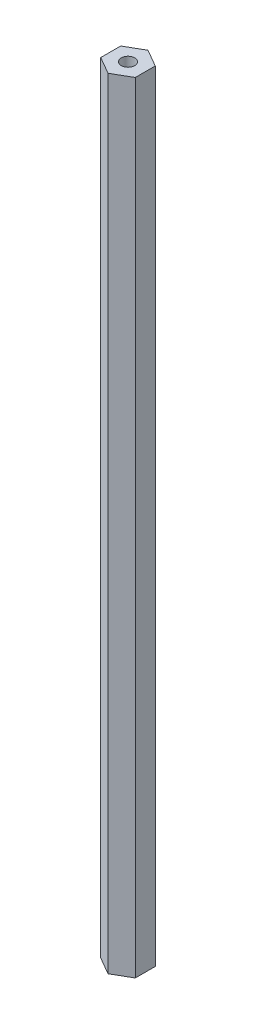
SolidWorks part; units mm, degrees
ref_plane "Front Plane" through (0, 0, 0) normal (0, 0, 1) x (1, 0, 0)
ref_plane "Top Plane" through (0, 0, 0) normal (0, 1, 0) x (1, 0, 0)
ref_plane "Right Plane" through (0, 0, 0) normal (1, 0, 0) x (0, 0, -1)
sketch "Sketch1" plane through (0, 0, 0) normal (0, 1, 0) x (1, 0, 0)
  line L0 (0, 7.3323) -> (0, 0) construction
  line L1 (0, 7.3323) -> (-6.35, 3.6662)
  line L2 (-6.35, 3.6662) -> (-6.35, -3.6662)
  line L3 (-6.35, -3.6662) -> (0, -7.3323)
  line L4 (0, -7.3323) -> (6.35, -3.6662)
  line L5 (6.35, -3.6662) -> (6.35, 3.6662)
  line L6 (6.35, 3.6662) -> (0, 7.3323)
  circle A0 centre (0, 0) radius 6.35 construction
  dimension "D1" = 12.7
extrude "Boss-Extrude1" add sketch "Sketch1" along normal blind 286.639
sketch "Sketch2" plane through (0, 286.639, 0) normal (0, 1, 0) x (1, 0, 0)
  line L2 (-6.35, 3.6662) -> (6.35, -3.6662) construction
  circle A0 centre (0, 0) radius 2.4892
  dimension "D1" = 4.9784
extrude "Cut-Extrude1" cut sketch "Sketch2" against normal blind 25.4
sketch "Sketch3" plane through (0, 0, 0) normal (0, -1, 0) x (-1, 0, 0)
  line L0 (6.35, -3.6662) -> (-6.35, 3.6662) construction
  circle A0 centre (0, 0) radius 2.4892
  dimension "D1" = 4.9784
extrude "Cut-Extrude2" cut sketch "Sketch3" against normal blind 25.4
